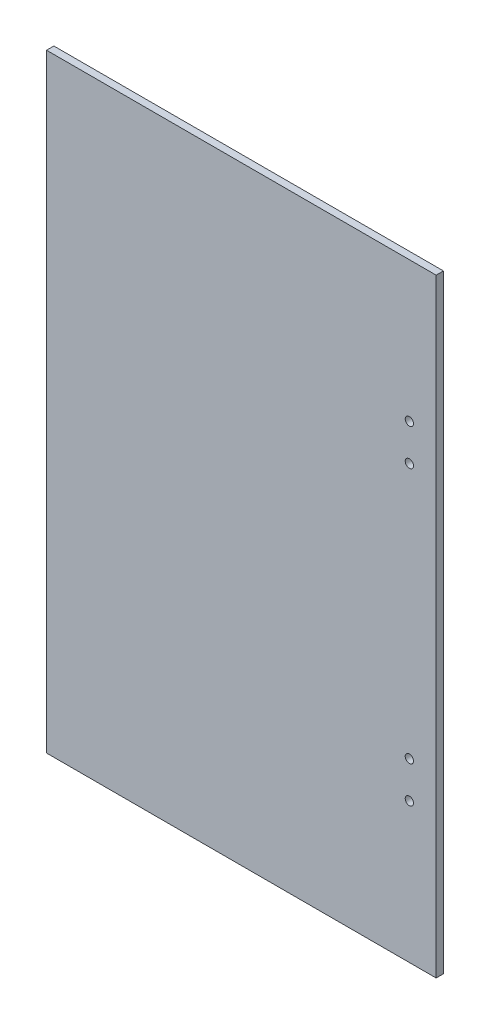
SolidWorks part; units mm, degrees
ref_plane "Plan de face" through (0, 0, 0) normal (0, 0, 1) x (1, 0, 0)
ref_plane "Plan de dessus" through (0, 0, 0) normal (0, 1, 0) x (1, 0, 0)
ref_plane "Plan de droite" through (0, 0, 0) normal (1, 0, 0) x (0, 0, -1)
sketch "Esquisse1" plane through (0, 0, 0) normal (0, 0, 1) x (1, 0, 0)
  line L1 (-80, -125) -> (80, -125)
  line L2 (-80, -125) -> (-80, 125)
  line L3 (-80, 125) -> (80, 125)
  line L4 (80, -125) -> (80, 125)
  line L5 (-80, -125) -> (80, 125) construction
  line L6 (-80, 125) -> (80, -125) construction
  point P0 (0, 0)
  dimension "D1" = 160
  dimension "D2" = 250
extrude "Boss.-Extru.1" add sketch "Esquisse1" along normal mid plane 3
sketch "Esquisse2" plane through (0, 0, 1.5) normal (0, 0, 1) x (1, 0, 0)
  line L0 (0, 0) -> (80, 0) construction
  line L1 (80, -125) -> (80, 125) construction
  line L2 (80, 60) -> (69, 60) construction
  line L3 (69, 67.5) -> (69, 52.5) construction
  circle A0 centre (69, 67.5) radius 1.7
  circle A1 centre (69, 52.5) radius 1.7
  circle A2 centre (69, -52.5) radius 1.7
  circle A3 centre (69, -67.5) radius 1.7
  point P10 (69, 60)
  point P12 (69, 52.5)
  point P13 (72.2789, 53.2547)
  dimension "D1" = 11
  dimension "D3" = 3.4
  dimension "D2" = 15
  dimension "D4" = 60
extrude "Enlèv. mat.-Extru.1" cut sketch "Esquisse2" against normal through all
